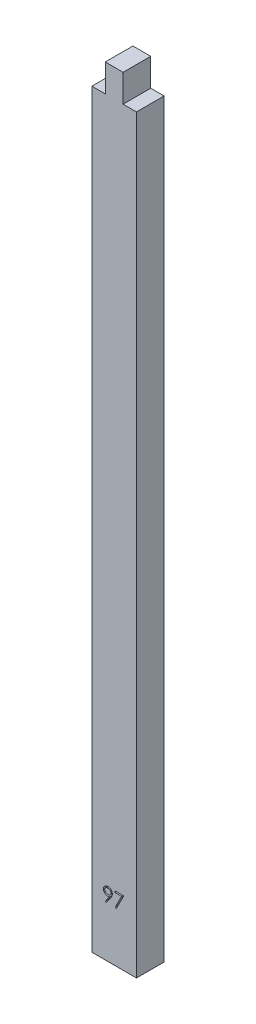
SolidWorks part; units mm, degrees
ref_plane "Front Plane" through (0, 0, 0) normal (0, 0, 1) x (1, 0, 0)
ref_plane "Top Plane" through (0, 0, 0) normal (0, 1, 0) x (1, 0, 0)
ref_plane "Right Plane" through (0, 0, 0) normal (1, 0, 0) x (0, 0, -1)
sketch "Sketch1" plane through (0, 0, 0) normal (0, 0, 1) x (1, 0, 0)
  line L0 (0, 0) -> (0, 168.21)
  line L2 (10, 168.21) -> (10, 0)
  line L3 (10, 0) -> (0, 0)
  line L4 (3, 174.41) -> (3, 168.21)
  line L6 (7, 168.21) -> (7, 174.41)
  line L8 (3, 174.41) -> (7, 174.41)
  line L9 (0, 168.21) -> (3, 168.21)
  line L10 (7, 168.21) -> (10, 168.21)
  dimension "D1" = 4
  dimension "D2" = 10
  dimension "D3" = 4
  dimension "D4" = 3
  dimension "D5" = 6.2
extrude "Boss-Extrude1" add sketch "Sketch1" along normal blind 6.2 contours L3 L0 L9 L4 L8 L6 L10 L2
sketch "Sketch3" plane through (0, 0, 0) normal (0, -1, 0) x (1, 0, 0)
  line L3 (10, 0) -> (10, 6.2)
  circle A0 centre (5, 3.15) radius 2.35
sketch "Sketch4" plane through (0, 0, 6.2) normal (0, 0, 1) x (1, 0, 0)
  text T0 "97"
extrude "Cut-Extrude1" cut sketch "Sketch4" against normal blind 1
